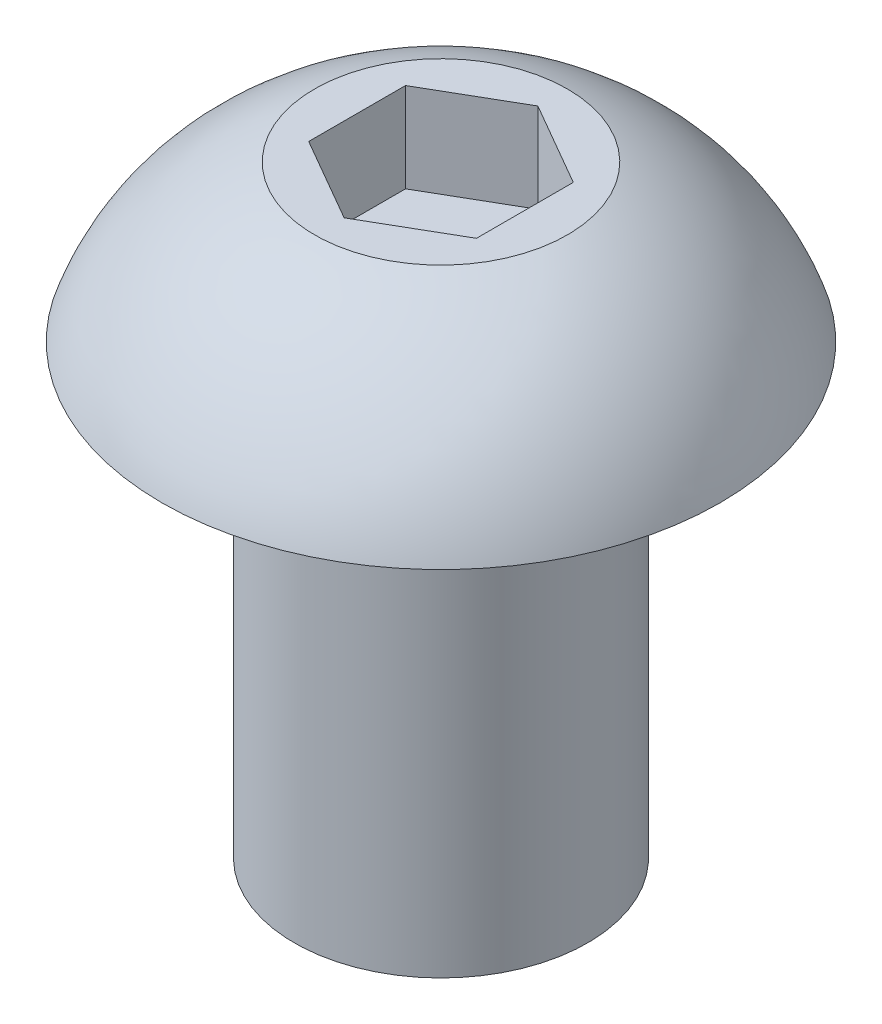
SolidWorks part; units mm, degrees
material "AISI Type 316L stainless steel"
ref_plane "Front Plane" through (0, 0, 0) normal (0, 0, 1) x (1, 0, 0)
ref_plane "Top Plane" through (0, 0, 0) normal (0, 1, 0) x (1, 0, 0)
ref_plane "Right Plane" through (0, 0, 0) normal (1, 0, 0) x (0, 0, -1)
sketch "Sketch1" plane through (0, 0, 0) normal (0, 0, 1) x (1, 0, 0)
  line L0 (-2.0828, 0) -> (-3.9624, 0)
  line L1 (-2.0828, 0) -> (-2.0828, -6.35)
  line L2 (0, -6.35) -> (0, 2.2098)
  line L3 (0, 2.2098) -> (-1.7948, 2.2098)
  line L4 (-2.0828, -6.35) -> (0, -6.35)
  arc A0 (-3.9624, 0) -> (-1.7948, 2.2098) centre (-0.5889, -1.1411) cw
  dimension "D1" = 6.35
  dimension "D2" = 2.2098
  dimension "D3" = 3.9624
  dimension "D4" = 2.0828
  dimension "D5" = 1.7948
revolve "Revolve1" add sketch "Sketch1" angle 360 about L2
sketch "Sketch2" plane through (0, 2.2098, 0) normal (0, 1, 0) x (1, 0, 0)
  line L0 (0, 0) -> (0, 1.3748) construction
  line L1 (-1.1906, 0.6874) -> (-1.1906, -0.6874)
  line L2 (-1.1906, -0.6874) -> (0, -1.3748)
  line L3 (0, -1.3748) -> (1.1906, -0.6874)
  line L4 (1.1906, -0.6874) -> (1.1906, 0.6874)
  line L5 (1.1906, 0.6874) -> (0, 1.3748)
  line L6 (0, 1.3748) -> (-1.1906, 0.6874)
  circle A0 centre (0, 0) radius 1.1906 construction
  dimension "D1" = 2.3813
extrude "Cut-Extrude1" cut sketch "Sketch2" against normal blind 1.27
